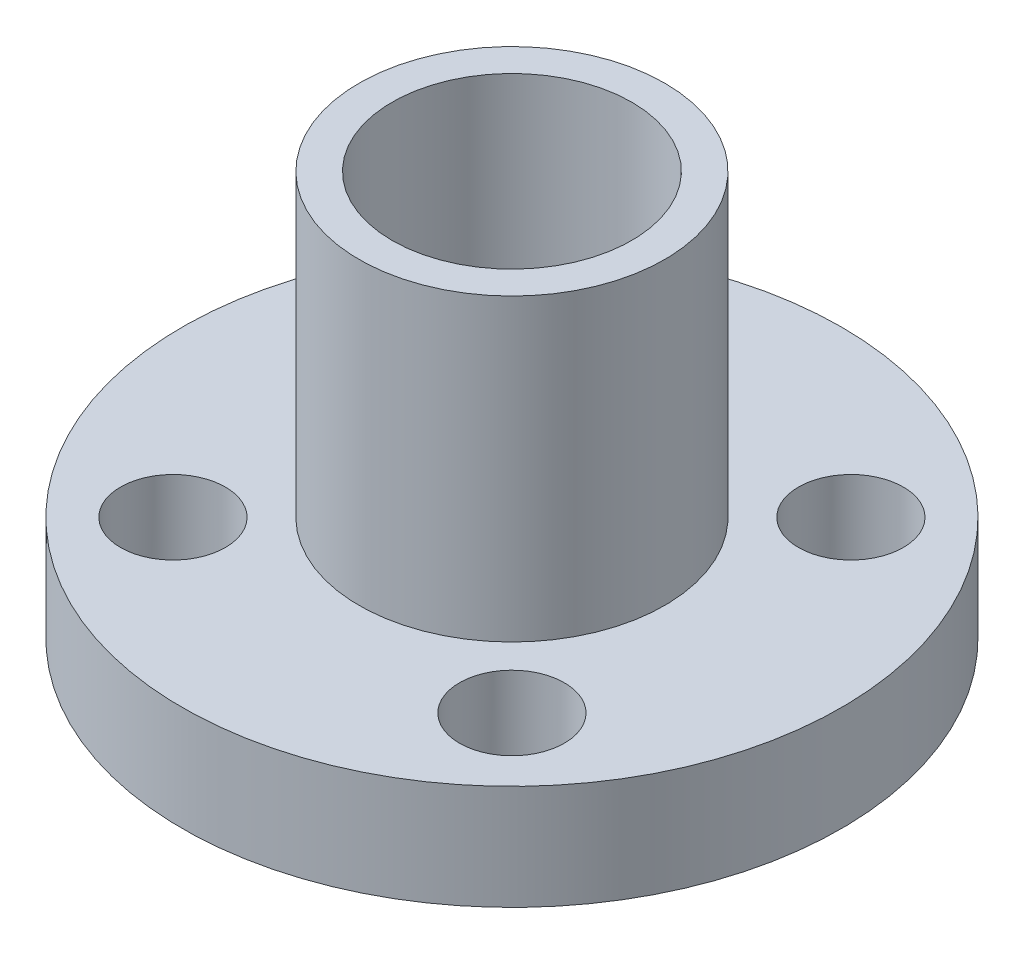
SolidWorks part; units mm, degrees
material "Brass"
ref_plane "Front Plane" through (0, 0, 0) normal (0, 0, 1) x (1, 0, 0)
ref_plane "Top Plane" through (0, 0, 0) normal (0, 1, 0) x (1, 0, 0)
ref_plane "Right Plane" through (0, 0, 0) normal (1, 0, 0) x (0, 0, -1)
sketch "Sketch1" plane through (0, 0, 0) normal (0, 0, 1) x (1, 0, 0)
  line L0 (0, 0) -> (0, 15)
  line L1 (0, 15) -> (5.1, 15)
  line L2 (5.1, 15) -> (5.1, 5)
  line L3 (5.1, 5) -> (11, 5)
  line L4 (11, 5) -> (11, 1.5)
  line L5 (11, 1.5) -> (5.1, 1.5)
  line L6 (5.1, 1.5) -> (5.1, 0)
  line L7 (5.1, 0) -> (0, 0)
  line L8 (5.1, 5) -> (5.1, 1.5) construction
  dimension "D1" = 1.5
  dimension "D2" = 3.5
  dimension "D3" = 10
  dimension "D4" = 5.1
  dimension "D5" = 11
revolve "Revolve1" add sketch "Sketch1" angle 360 about L0
hole_wizard "Ø3.5 (3.5) Diameter Hole1" positions "Sketch3" profile "Sketch2" hole size "Ø3.5" standard "ANSI Metric"
sketch "Sketch3" plane through (0, 5, 0) normal (0, 1, 0) x (1, 0, 0)
  line L1 (-5.6569, 5.6569) -> (5.6569, 5.6569) construction
  line L2 (-5.6569, 5.6569) -> (-5.6569, -5.6569) construction
  line L3 (-5.6569, -5.6569) -> (5.6569, -5.6569) construction
  line L4 (5.6569, 5.6569) -> (5.6569, -5.6569) construction
  line L5 (-5.6569, 5.6569) -> (5.6569, -5.6569) construction
  line L6 (-5.6569, -5.6569) -> (5.6569, 5.6569) construction
  point P0 (-5.6569, -5.6569)
  point P2 (5.6569, -5.6569)
  point P4 (5.6569, 5.6569)
  point P6 (-5.6569, 5.6569)
  point P9 (0, 0)
  dimension "D1" = 8
sketch "Sketch2" plane through (-5.6569, 5, 5.6569) normal (1, 0, 0) x (0, 0, 1)
  line L0 (0, 0) -> (0, 5)
  line L1 (0, 5) -> (1.75, 5)
  line L2 (1.75, 5) -> (1.75, 0)
  line L5 (1.75, 0) -> (0, 0)
  line L11 (0, -6.35) -> (0, 107.95) construction
  dimension "Thru Hole Dia." = 3.5
  dimension "Thru Hole Depth" = 5
hole_wizard "Ø8.0 (8) Diameter Hole1" positions "Sketch5" profile "Sketch4" hole size "Ø8.0" standard "ANSI Metric" end condition through all
sketch "Sketch5" plane through (0, 15, 0) normal (0, 1, 0) x (1, 0, 0)
  point P0 (0, 0)
sketch "Sketch4" plane through (0, 15, 0) normal (1, 0, 0) x (0, 0, 1)
  line L0 (0, 0) -> (0, 15)
  line L1 (0, 15) -> (4, 15)
  line L2 (4, 15) -> (4, 0)
  line L5 (4, 0) -> (0, 0)
  line L11 (0, -6.35) -> (0, 107.95) construction
  dimension "Thru Hole Dia." = 8
  dimension "Thru Hole Depth" = 15
